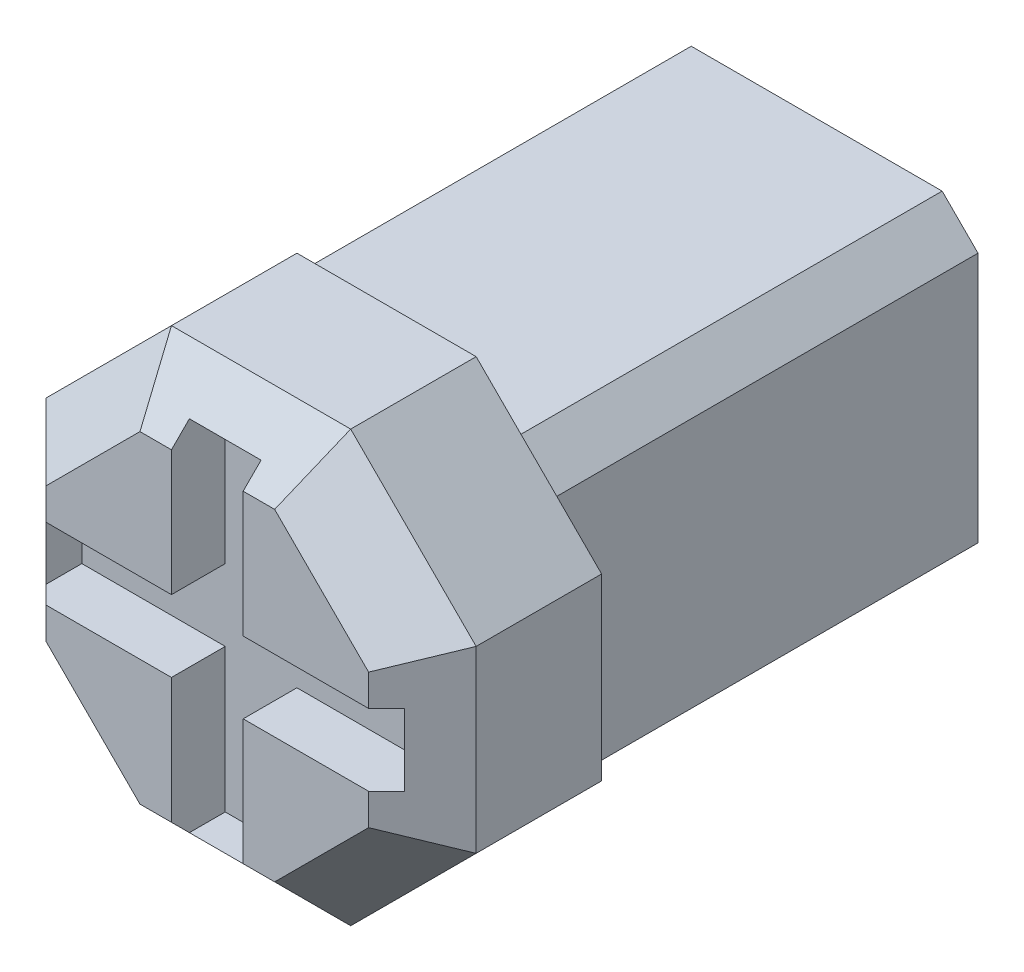
SolidWorks part; units mm, degrees
ref_plane "Plan de face" through (0, 0, 0) normal (0, 0, 1) x (1, 0, 0)
ref_plane "Plan de dessus" through (0, 0, 0) normal (0, 1, 0) x (1, 0, 0)
ref_plane "Plan de droite" through (0, 0, 0) normal (1, 0, 0) x (0, 0, -1)
sketch "Esquisse1" plane through (0, 0, 0) normal (0, 0, 1) x (1, 0, 0)
  line L0 (0, 0) -> (-4.5, 0) construction
  line L1 (-4.5, 4.5) -> (4.5, 4.5)
  line L2 (-4.5, 4.5) -> (-4.5, -4.5)
  line L3 (-4.5, -4.5) -> (4.5, -4.5)
  line L4 (4.5, 4.5) -> (4.5, -4.5)
  line L5 (0, 0) -> (0, -4.5) construction
  dimension "D1" = 9
  dimension "D2" = 9
extrude "Extrusion1" add sketch "Esquisse1" along normal blind 12
sketch "Esquisse2" plane through (0, 0, 12) normal (0, 0, 1) x (1, 0, 0)
  line L8 (-6, 6) -> (-6, -6)
  line L9 (-6, -6) -> (6, -6)
  line L10 (6, -6) -> (6, 6)
  line L11 (6, 6) -> (-6, 6)
  line L12 (-6, 6) -> (-6, -6)
  line L13 (-6, -6) -> (6, -6)
  line L14 (6, -6) -> (6, 6)
  line L15 (6, 6) -> (-6, 6)
  dimension "D2" = 12
  dimension "D1" = 1.5
extrude "Extrusion2" add sketch "Esquisse2" along normal blind 5
chamfer "Chanfrein3" distance 1 angle 45 4 edges at (-4.5, 4.5, 6) (4.5, 4.5, 6) (4.5, -4.5, 6) (-4.5, -4.5, 6)
chamfer "Chanfrein1" distance 3.5 angle 45 4 edges at (6, 6, 14.5) (-6, 6, 14.5) (-6, -6, 14.5) (6, -6, 14.5)
chamfer "Chanfrein2" distance 1.5 angle 45 8 edges at (0, 6, 17) (6, 0, 17) (-6, 0, 17) (0, -6, 17) (-4.25, 4.25, 17) (-4.25, -4.25, 17) (4.25, -4.25, 17) (4.25, 4.25, 17)
sketch "Esquisse3" plane through (0, 0, 17) normal (0, 0, 1) x (1, 0, 0)
  line L1 (-1, 5) -> (1, 5)
  line L2 (-1, 5) -> (-1, -5)
  line L3 (-1, -5) -> (1, -5)
  line L4 (1, 5) -> (1, -5)
  line L5 (-5, 1) -> (5, 1)
  line L6 (-5, 1) -> (-5, -1)
  line L7 (-5, -1) -> (5, -1)
  line L8 (5, 1) -> (5, -1)
  line M1 (-1.8787, -4.5) -> (1.8787, -4.5)
  line M3 (4.5, -1.8787) -> (4.5, 1.8787)
  line M5 (1.8787, 4.5) -> (-1.8787, 4.5)
  line M7 (-4.5, 1.8787) -> (-4.5, -1.8787)
  dimension "D1" = 10
  dimension "D2" = 2
  dimension "D3" = 1
  dimension "D4" = 1
  dimension "D5" = 5
  dimension "D6" = 5
extrude "Enlèv. mat.-Extru.1" cut sketch "Esquisse3" against normal blind 1.5 contours L2 L5 L4 M5 | L7 L2 L5 M7 | L2 L7 L4 L5 | L7 L2 L4 M1 | L4 L7 L5 M3 | L6 L7 L5 M7 | L4 L1 L2 M5 | L4 L2 L3 M1 | L8 L5 L7 M3
